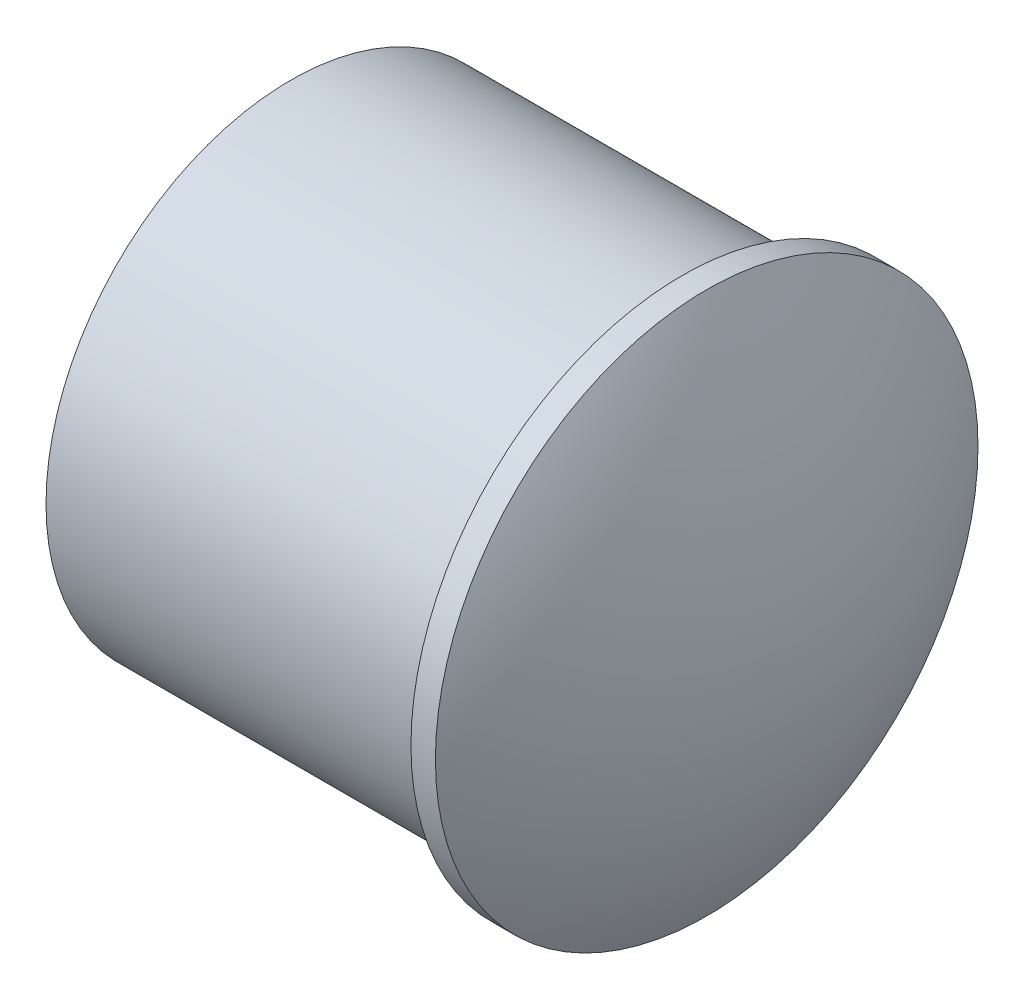
SolidWorks part; units mm, degrees
ref_plane "Front Plane" through (0, 0, 0) normal (0, 0, 1) x (1, 0, 0)
ref_plane "Top Plane" through (0, 0, 0) normal (0, 1, 0) x (1, 0, 0)
ref_plane "Right Plane" through (0, 0, 0) normal (1, 0, 0) x (0, 0, -1)
sketch "Sketch1" plane through (0, 0, 0) normal (0, 0, 1) x (1, 0, 0)
  line L0 (0, 0) -> (0, 10)
  line L1 (0, 10) -> (16, 10)
  line L2 (16, 10) -> (16, 11.0867)
  line L3 (16, 11.0867) -> (17, 11.0867)
  line L4 (0, 0) -> (20, 0)
  arc A0 (17, 11.0867) -> (20, 0) centre (-3.0341, -0.2837) cw
  point P8 (17.3758, 11.0867)
  dimension "D1" = 20
  dimension "D2" = 10
  dimension "D3" = 16
  dimension "D4" = 1
revolve "Revolve1" add sketch "Sketch1" angle 360 about L4
